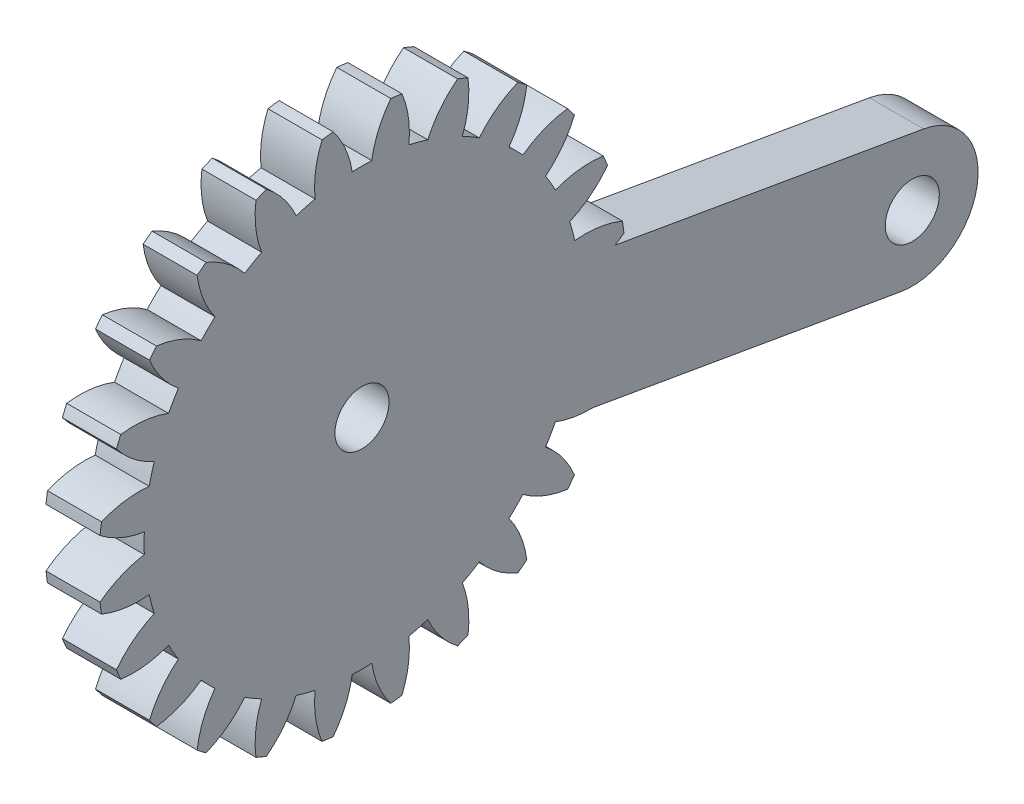
SolidWorks part; units mm, degrees
material "1060 Alloy"
ref_plane "Plane1" through (0, 0, 0) normal (0, 0, 1) x (1, 0, 0)
ref_plane "Plane2" through (0, 0, 0) normal (0, 1, 0) x (1, 0, 0)
ref_plane "Plane3" through (0, 0, 0) normal (1, 0, 0) x (0, 0, -1)
sketch "HoldingSke" plane through (0, 0, 0) normal (0, 1, 0) x (1, 0, 0)
  line L0 (0, 0) -> (0.812, -0.3615)
  line L1 (-15, 0) -> (100, 0) construction
  line L2 (0, 0) -> (-2.1039, 2.3779)
  line L3 (0, 0) -> (-11.863, 4.5341)
  line L4 (0, 0) -> (7.8894, 3.5126)
  line L5 (0, 0) -> (-46.8476, -17.4728)
  line L6 (0, 0) -> (-2.4869, -1.6779)
  line L7 (-2.1039, 2.3779) -> (8.6586, 51.2059)
  line L8 (-76.2, 54.61) -> (-76, 54.61)
  line L9 (-71.009, 38.7566) -> (-53.1078, 45.2721)
  line L10 (-76.2, 71.12) -> (104.1128, 71.12)
  line L11 (0, 0) -> (-3, 0)
  line L12 (-76.2, 101.6) -> (-76.158, 101.6)
  line L13 (24.9733, 27.94) -> (52.9518, 28.4284)
  line L14 (24.9733, 27.94) -> (24.9743, 27.94)
  line L15 (24.9733, 27.94) -> (100.4006, 29.5858)
  line L16 (-63.627, -1.125) -> (-12.827, -1.125)
  circle A0 centre (0, 0) radius 0.75
  circle A1 centre (0, 0) radius 12.0928
  circle A2 centre (0, 0) radius 37.5
  circle A3 centre (0, 0) radius 0.75
  dimension "MHD" = 24.1855
  dimension "Hub_dia" = 75
  dimension "Bore" = 1.5
  dimension "MBD" = 1.5
  dimension "Num_teeth" = 24
  dimension "Pitch_radius" = 180.3128
  dimension "Pitch" = 0.8889
  dimension "Width" = 3
  dimension "Overall_len" = 50
  dimension "Show_teeth" = 24
  dimension "Thickness" = 3
  dimension "OAL" = 50.0001
  dimension "T_dim" = 0.2
  dimension "Ap" = 20
  dimension "H" = 19.05
  dimension "Backlash" = 0.042
  dimension "Addendum_fac" = 1
  dimension "Dedendum_fac" = 1.25
  dimension "Clearance_fac" = 0.25
  dimension "Dedendum_add" = 0.001
  dimension "Module" = 1.125
sketch "BasProSke" plane through (0, 0, 0) normal (0, 1, 0) x (1, 0, 0)
  line L0 (-10, 0) -> (60, 0) construction
  line L1 (0, 0) -> (0, 14.625)
  line L2 (0, 0) -> (3, 0)
  line L3 (3, 0) -> (3, 14.625)
  line L4 (3, 14.625) -> (0, 14.625)
  dimension "Diameter" = 29.25
  dimension "Thickness" = 3
revolve "Base-Revolve" add sketch "BasProSke" angle 360 about L0
sketch "TooCutSke" plane through (0, 0, 0) normal (1, 0, 0) x (0, 0, -1)
  line L1 (0, 0) -> (0, 107) construction
  line L2 (0, 0) -> (-0.9564, 13.4661) construction
  line L3 (0, 0) -> (-3.5179, 26.7209) construction
  line L4 (-0.9564, 13.4661) -> (-1.7589, 13.3604) construction
  arc A0 (0.5427, 12.0806) -> (-0.5427, 12.0806) centre (0, 0) ccw
  arc A1 (1.6173, 14.5609) -> (-1.6173, 14.5609) centre (0, 0) ccw
  circle A2 centre (0, 0) radius 13.5 construction
  circle A3 centre (0, 0) radius 12.6859 construction
  arc A4 (-0.5427, 12.0806) -> (-1.6173, 14.5609) centre (-5.8773, 11.2423) ccw
  arc A5 (1.6173, 14.5609) -> (0.5427, 12.0806) centre (5.8773, 11.2423) ccw
  dimension "Root_dia" = 24.1855
  dimension "Overcut_dia" = 29.3008
  dimension "Pitch_dia" = 27
  dimension "Base_dia" = 25.3717
  dimension "Flank_rad" = 5.4
  dimension "Half_ang" = 7.5
  dimension "Half_CT" = 0.8094
extrude "ToothCut" cut sketch "TooCutSke" along normal through all
fillet "Breaks" [suppressed] radius 0.0225
fillet "RootFillets" [suppressed] radius 0.2823
pattern_circular "TeethCuts" count 24 every 15 about axis through (-10, 0, 0) along (1, 0, 0) of "ToothCut", "RootFillets", "Breaks"
sketch "HubNeaOneSke" plane through (0, 0, 0) normal (-1, 0, 0) x (0, 0, 1)
  circle A0 centre (0, 0) radius 12.0928
  dimension "Diameter" = 24.1855
extrude "HubNearOne" [suppressed] add sketch "HubNeaOneSke" along normal blind 47.0001
sketch "HubNeaBotSke" plane through (0, 0, 0) normal (-1, 0, 0) x (0, 0, 1)
  circle A0 centre (0, 0) radius 12.0928
  dimension "Diameter" = 24.1855
extrude "HubNearBoth" [suppressed] add sketch "HubNeaBotSke" along normal blind 23.5
ref_plane "FarPln" through (3, 0, 0) normal (1, 0, 0) x (0, 0, -1)
sketch "HubFarSke" plane through (3, 0, 0) normal (1, 0, 0) x (0, 0, -1)
  circle A0 centre (0, 0) radius 12.0928
  dimension "Diameter" = 24.1855
extrude "HubFar" [suppressed] add sketch "HubFarSke" along normal blind 23.5
sketch "BorSke" plane through (0, 0, 0) normal (1, 0, 0) x (0, 0, -1)
  circle A0 centre (0, 0) radius 1.5
  dimension "Diameter" = 3
extrude "Bore" cut sketch "BorSke" along normal mid plane 100.0001
sketch "KeySke" plane through (0, 0, 0) normal (1, 0, 0) x (0, 0, -1)
  line L0 (-0.3, 0) -> (-0.3, 0.95)
  line L1 (-0.3, 0.95) -> (0.3, 0.95)
  line L2 (0.3, 0.95) -> (0.3, 0)
  line L3 (0, 0) -> (0, 34) construction
  line L4 (-0.3, 0) -> (0.3, 0)
  dimension "Offset" = 0.95
  dimension "Width" = 0.6
extrude "Keyway" [suppressed] cut sketch "KeySke" along normal mid plane 100.0001
pattern_circular "Keyway2" [suppressed] count 2 every 90 about axis through (-10, 0, 0) along (1, 0, 0)
sketch "Sketch1" plane through (0, 0, 0) normal (1, 0, 0) x (0, 0, -1)
  line L0 (31.1674, -1.709) -> (11.9832, 1.6238)
  line L1 (10.7334, -5.5703) -> (29.9176, -8.9031)
  line L2 (0, 0) -> (30.5425, -5.306) construction
  line L3 (10.7334, -5.5703) -> (11.9832, 1.6238)
  arc A0 (29.9176, -8.9031) -> (31.1674, -1.709) centre (30.5425, -5.306) ccw
  circle A1 centre (30.5425, -5.306) radius 1.5
  point P6 (0, 0)
  dimension "D2" = 3
  dimension "D3" = 3.6509
  dimension "D1" = 31
extrude "Boss-Extrude1" add sketch "Sketch1" along normal blind 3
equation "' \"Module@HoldingSke\" = 6.35"
equation "' \"Num_teeth@HoldingSke\" = 12"
equation "' \"Ap@HoldingSke\" =  20"
equation "' \"Width@HoldingSke\" = 0.5 * 25.4"
equation "' \"Hub_dia@HoldingSke\"= 1 * 25.4"
equation "' \"Overall_len@HoldingSke\" = 1.0 * 25.4"
equation "' \"Bore@HoldingSke\" = 0.75 * 25.4"
equation "' \"T_dim@HoldingSke\" = 0.1 * 25.4"
equation "' \"Width@KeySke\" = 0.25 * 25.4"
equation "' \"Show_teeth@HoldingSke\" = 13"
equation "' \"Backlash@HoldingSke\" = 0.009 * 25.4"
equation "' \"Addendum_fac@HoldingSke\" = 1.0"
equation "' \"Dedendum_fac@HoldingSke\" = 1.25"
equation "' \"Dedendum_add@HoldingSke\" = 0.00005 * 25.4"
equation "' \"Clearance_fac@HoldingSke\" = 0.25"
equation "\"Pitch@HoldingSke\" = 1 / \"Module@HoldingSke\""
equation "\"Overcut_dia@TooCutSke\" = (\"Num_teeth@HoldingSke\" + 2 * \"Addendum_fac@HoldingSke\") / \"Pitch@HoldingSke\" + 0.002 * 25.4"
equation "\"Pitch_dia@TooCutSke\" = \"Num_teeth@HoldingSke\" / \"Pitch@HoldingSke\""
equation "\"Base_dia@TooCutSke\" = \"Num_teeth@HoldingSke\" / \"Pitch@HoldingSke\" * cos((\"Ap@HoldingSke\"  * 3.14159265 / 180))"
equation "\"Root_dia@TooCutSke\" = (\"Num_teeth@HoldingSke\" + 2) / \"Pitch@HoldingSke\" - 2 * (\"Addendum_fac@HoldingSke\" + \"Dedendum_fac@HoldingSke\") / \"Pitch@HoldingSke\" - \"Dedendum_add@HoldingSke\" * 2"
equation "\"Half_ang@TooCutSke\" = 180 / \"Num_teeth@HoldingSke\""
equation "\"Half_CT@TooCutSke\" = \"Num_teeth@HoldingSke\" / \"Pitch@HoldingSke\" * sin((3.14159265 / 2 / \"Num_teeth@HoldingSke\")) / 2 - 7 * \"Backlash@HoldingSke\" / 4"
equation "\"Flank_rad@TooCutSke\" = \"Num_teeth@HoldingSke\" / \"Pitch@HoldingSke\" / 5"
equation "\"Radius@RootFillets\" = \"Clearance_fac@HoldingSke\" / \"Pitch@HoldingSke\" + \"Dedendum_add@HoldingSke\""
equation "\"Break_rad@Breaks\" = 0.02 / \"Pitch@HoldingSke\""
equation "\"Thickness@HoldingSke\" = \"Width@HoldingSke\""
equation "\"OAL@HoldingSke\" = \"Thickness@HoldingSke\""
equation "\"MHD@HoldingSke\" = (\"Num_teeth@HoldingSke\" + 2) / \"Pitch@HoldingSke\" - 2 * (\"Addendum_fac@HoldingSke\" + \"Dedendum_fac@HoldingSke\")  / \"Pitch@HoldingSke\" - \"Dedendum_add@HoldingSke\" * 2"
equation "\"MBD@HoldingSke\" = (\"Num_teeth@HoldingSke\" + 2) / \"Pitch@HoldingSke\" - 2 * (\"Addendum_fac@HoldingSke\" + \"Dedendum_fac@HoldingSke\")  / \"Pitch@HoldingSke\" - \"Dedendum_add@HoldingSke\" * 2 - 0.002 * 25.4"
equation "\"MHD@HoldingSke\" = ((sgn( \"MHD@HoldingSke\" - \"Hub_dia@HoldingSke\" )-1)*( \"MHD@HoldingSke\" - \"Hub_dia@HoldingSke\" ))/-2+ \"Hub_dia@HoldingSke\""
equation "\"MBD@HoldingSke\" = ((sgn( \"MBD@HoldingSke\" - \"Bore@HoldingSke\" )-1)*( \"MBD@HoldingSke\" - \"Bore@HoldingSke\" ))/-2+ \"Bore@HoldingSke\""
equation "\"OAL@HoldingSke\" = ((sgn( \"OAL@HoldingSke\" - \"Overall_len@HoldingSke\" )+1)*( \"OAL@HoldingSke\" - \"Overall_len@HoldingSke\" ))/2 + \"Overall_len@HoldingSke\" + 0.000002 * 25.4"
equation "\"Num_teeth@TeethCuts\" = int( \"Show_teeth@HoldingSke\" ) + 1"
equation "\"Num_teeth@TeethCuts\" = ((sgn( \"Num_teeth@TeethCuts\" - \"Num_teeth@HoldingSke\" )-1)*( \"Num_teeth@TeethCuts\" - \"Num_teeth@HoldingSke\" ))/-2+ \"Num_teeth@HoldingSke\""
equation "\"Num_teeth@TeethCuts\" = ((sgn( \"Num_teeth@TeethCuts\" - 2.0)+1)*( \"Num_teeth@TeethCuts\" - 2.0))/2 +2.0"
equation "\"Angle@TeethCuts\" = 360.0 / \"Num_teeth@HoldingSke\""
equation "\"Diameter@BasProSke\" = (\"Num_teeth@HoldingSke\" + 2 * \"Addendum_fac@HoldingSke\") / \"Pitch@HoldingSke\""
equation "\"Thickness@BasProSke\"  = \"Thickness@HoldingSke\""
equation "' \"Fillet_rad@BasProSke\" =  \"Thickness@HoldingSke\" * 0.05"
equation "\"MHD@HoldingSke\" = ((sgn( \"MHD@HoldingSke\" - \"Root_dia@TooCutSke\" )-1)*( \"MHD@HoldingSke\" - \"Root_dia@TooCutSke\" ))/-2+ \"Root_dia@TooCutSke\""
equation "\"Diameter@HubNeaOneSke\" = \"MHD@HoldingSke\""
equation "\"Length@HubNearOne\" = \"OAL@HoldingSke\" - \"Thickness@BasProSke\""
equation "\"Diameter@HubNeaBotSke\" = \"MHD@HoldingSke\""
equation "\"Length@HubNearBoth\" = ( \"OAL@HoldingSke\" - \"Thickness@BasProSke\" ) / 2.0"
equation "\"Thickness@FarPln\" = \"Thickness@BasProSke\""
equation "\"Diameter@HubFarSke\" = \"MHD@HoldingSke\""
equation "\"Length@HubFar\" = ( \"OAL@HoldingSke\" - \"Thickness@BasProSke\" ) / 2.0"
equation "\"D1@Bore\" = \"OAL@HoldingSke\" * 2.0"
equation "\"D1@Keyway\" = \"OAL@HoldingSke\" * 2.0"
equation "\"Offset@KeySke\" = \"T_dim@HoldingSke\" + \"MBD@HoldingSke\" / 2.0"
